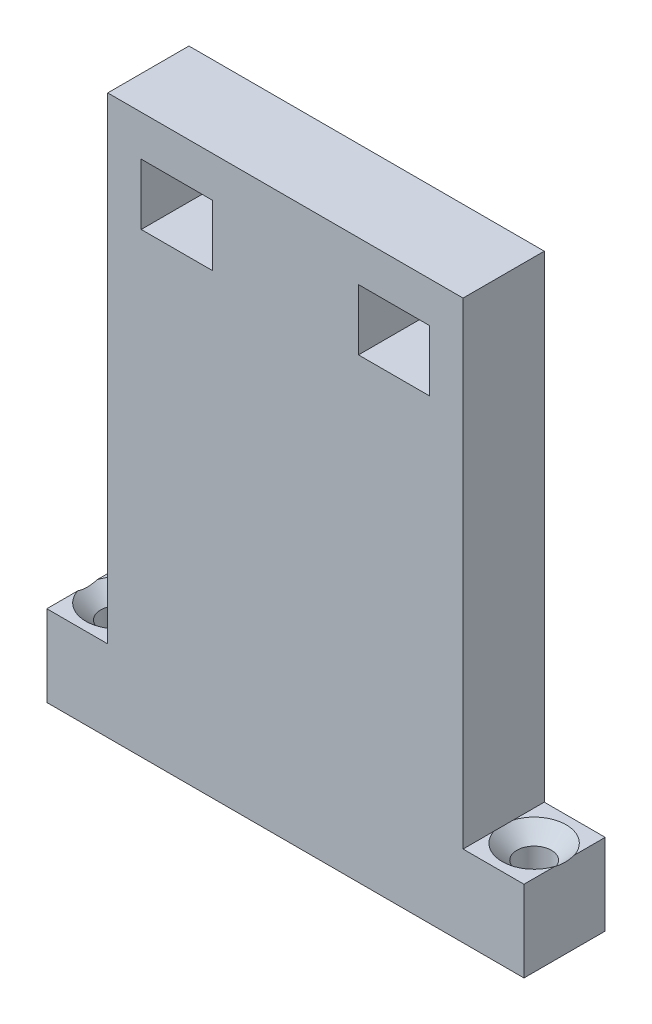
SolidWorks part; units mm, degrees
material "Nylon 6/10"
ref_plane "Front Plane" through (0, 0, 0) normal (0, 0, 1) x (1, 0, 0)
ref_plane "Top Plane" through (0, 0, 0) normal (0, 1, 0) x (1, 0, 0)
ref_plane "Right Plane" through (0, 0, 0) normal (1, 0, 0) x (0, 0, -1)
sketch "Sketch2" plane through (0, 0, 0) normal (0, 0, 1) x (1, 0, 0)
  line L0 (23.5, 0) -> (-23.5, 0)
  line L1 (-23.5, 0) -> (-23.5, 8)
  line L2 (-23.5, 8) -> (-17.5, 8)
  line L3 (-17.5, 8) -> (-17.5, 55)
  line L4 (-17.5, 55) -> (17.5, 55)
  line L5 (0, 56.8533) -> (0, -18.24) construction
  line L6 (7.2, 51) -> (7.2, 45)
  line L7 (-14.2, 51) -> (-7.2, 51)
  line L8 (-14.2, 51) -> (-14.2, 45)
  line L9 (-14.2, 45) -> (-7.2, 45)
  line L10 (-7.2, 51) -> (-7.2, 45)
  line L11 (14.2, 45) -> (7.2, 45)
  line L12 (14.2, 51) -> (14.2, 45)
  line L13 (14.2, 51) -> (7.2, 51)
  line L14 (17.5, 8) -> (17.5, 55)
  line L15 (23.5, 8) -> (17.5, 8)
  line L16 (23.5, 0) -> (23.5, 8)
  point P13 (0, 55)
  point P19 (0, 55)
  point P22 (0, 0)
  dimension "D1" = 8
  dimension "D2" = 6
  dimension "D3" = 35
  dimension "D4" = 55
  dimension "D5" = 7
  dimension "D6" = 14.4
  dimension "D7" = 45
  dimension "D8" = 6
extrude "Boss-Extrude1" add sketch "Sketch2" along normal blind 8
hole_wizard "CSK for M3 Flat Head Machine Screw1" positions "Sketch3" profile "Sketch4" countersink size "M3" standard "ANSI Metric"
sketch "Sketch3" plane through (0, 8, 0) normal (0, 1, 0) x (1, 0, 0)
  line L0 (-23.5, -4) -> (26.1328, -4) construction
  line L1 (-23.5, -8) -> (-23.5, 0) construction
  line L3 (-20.5, 0) -> (-20.5, -10.1118) construction
  line L4 (-17.5, 0) -> (-23.5, 0) construction
  line L6 (20.5, 0) -> (20.5, -12.2895) construction
  line L7 (23.5, 0) -> (17.5, 0) construction
  line L9 (-25.5, -4) -> (-15.5, -4) construction
  point P0 (-20.5, -4)
  point P2 (20.5, -4)
sketch "Sketch4" plane through (-20.5, 8, 4) normal (1, 0, 0) x (0, 0, 1)
  line L0 (0, 0) -> (0, 8)
  line L1 (0, 8) -> (1.7, 8)
  line L2 (1.7, 8) -> (1.7, 1.45)
  line L3 (1.7, 1.45) -> (3.15, 0)
  line L5 (3.15, 0) -> (0, 0)
  line L6 (-1.7, 1.45) -> (-3.15, 0) construction
  line L11 (0, -6.35) -> (0, 107.95) construction
  dimension "Thru Hole Dia." = 3.4
  dimension "Thru Hole Depth" = 8
  dimension "Near C'Sink Dia." = 6.3
  dimension "Near C'Sink Angle" = 90
